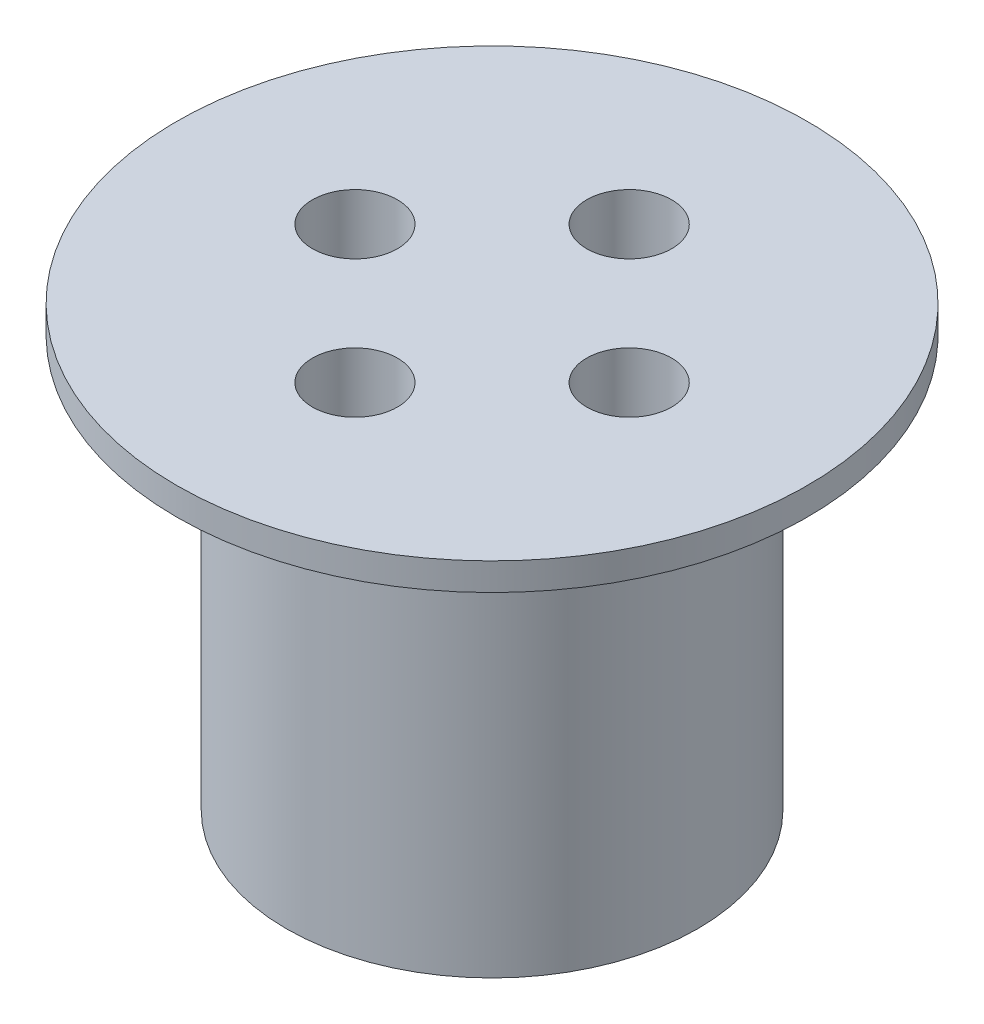
SolidWorks part; units mm, degrees
ref_plane "Front Plane" through (0, 0, 0) normal (0, 0, 1) x (1, 0, 0)
ref_plane "Top Plane" through (0, 0, 0) normal (0, 1, 0) x (1, 0, 0)
ref_plane "Right Plane" through (0, 0, 0) normal (1, 0, 0) x (0, 0, -1)
sketch "Sketch1" plane through (0, 0, 0) normal (0, 1, 0) x (1, 0, 0)
  circle A0 centre (0, 0) radius 15
extrude "Boss-Extrude1" add sketch "Sketch1" along normal blind 30
sketch "Sketch2" plane through (0, 30, 0) normal (0, 1, 0) x (1, 0, 0)
  circle A0 centre (0, 0) radius 23
  dimension "D1" = 46
extrude "Boss-Extrude2" add sketch "Sketch2" along normal blind 2
sketch "Sketch3" plane through (0, 0, 0) normal (0, -1, 0) x (1, 0, 0)
  circle A0 centre (0, 0) radius 10 construction
  circle A1 centre (0, 10) radius 2.25
  circle A2 centre (10, 0) radius 2.25
  circle A3 centre (0, -10) radius 2.25
  circle A4 centre (-10, 0) radius 2.25
  point P14 (0, 0)
  dimension "D1" = 4
  dimension "D2" = 20
  dimension "D3" = 4.5
extrude "Cut-Extrude1" cut sketch "Sketch3" against normal blind 10
sketch "Sketch4" plane through (0, 32, 0) normal (0, 1, 0) x (1, 0, 0)
  circle A0 centre (0, 0) radius 15 construction
  circle A1 centre (0, 0) radius 10 construction
  circle A2 centre (0, 10) radius 3.1
  circle A3 centre (10, 0) radius 3.1
  circle A4 centre (0, -10) radius 3.1
  circle A5 centre (-10, 0) radius 3.1
  point P15 (0, 0)
  dimension "D1" = 4
extrude "Cut-Extrude2" cut sketch "Sketch4" against normal blind 10
